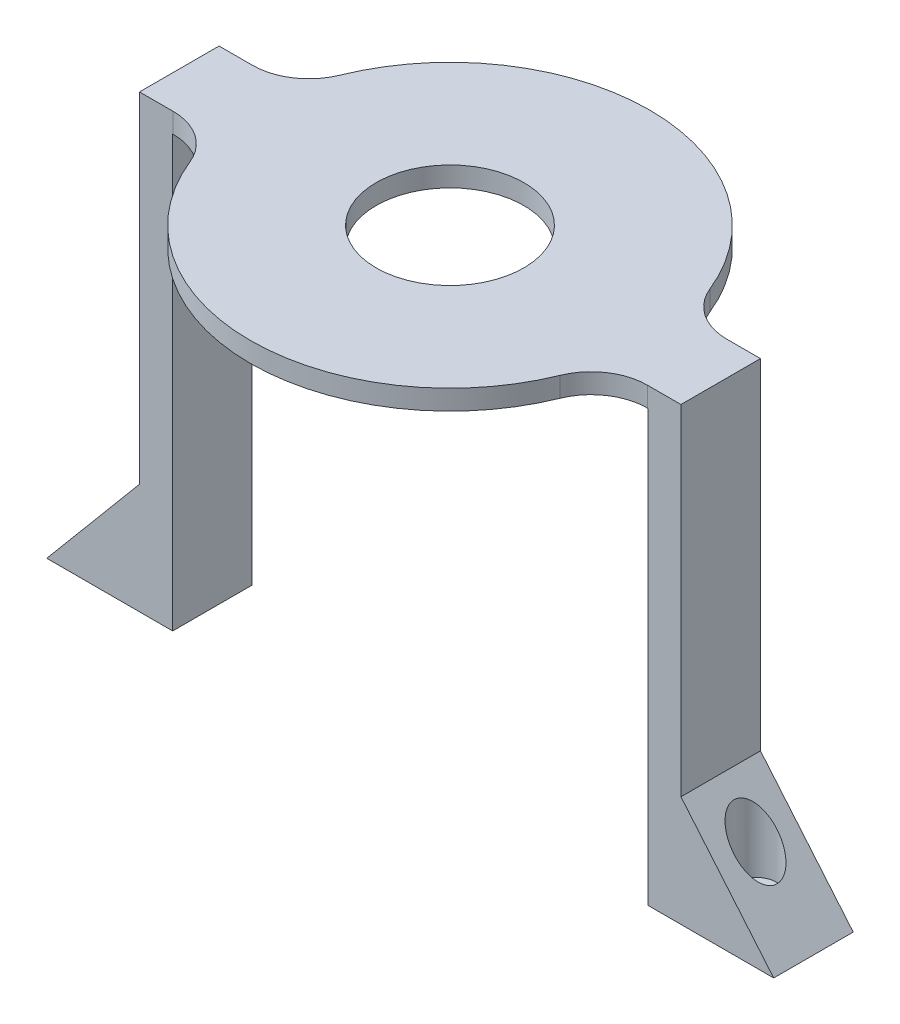
SolidWorks part; units mm, degrees
ref_plane "Front Plane" through (0, 0, 0) normal (0, 0, 1) x (1, 0, 0)
ref_plane "Top Plane" through (0, 0, 0) normal (0, 1, 0) x (1, 0, 0)
ref_plane "Right Plane" through (0, 0, 0) normal (1, 0, 0) x (0, 0, -1)
sketch "Sketch8" plane through (0, 0, 0) normal (0, 1, 0) x (1, 0, 0)
  line L0 (-35.85, 0) -> (35.85, 0) construction
  line L1 (-35.85, -6) -> (-29.5214, -6)
  line L2 (-35.85, 6) -> (-29.5214, 6)
  line L3 (29.5214, 6) -> (35.85, 6)
  line L4 (-35.85, 6) -> (35.85, 6) construction
  line L5 (29.5214, -6) -> (35.85, -6)
  line L6 (-35.85, -6) -> (35.85, -6) construction
  line L7 (-35.85, 6) -> (-35.85, -6)
  line L8 (35.85, 6) -> (35.85, -6)
  circle A0 centre (0, 0) radius 11.15
  arc A1 (29.5214, 6) -> (-29.5214, 6) centre (0, 0) ccw
  arc A2 (-29.5214, -6) -> (29.5214, -6) centre (0, 0) ccw
  point P6 (0, 0)
  dimension "D1" = 60.25
  dimension "D2" = 22.3
  dimension "D3" = 71.7
  dimension "D4" = 6
  dimension "D5" = 6
extrude "Boss-Extrude4" add sketch "Sketch8" along normal blind 3
sketch "Sketch9" plane through (0, 0, 6) normal (0, 0, 1) x (1, 0, 0)
  line L0 (-35.85, 3) -> (-35.85, -64.95)
  line L1 (-35.85, -64.95) -> (-54.85, -64.95)
  line L2 (-54.85, -64.95) -> (-40.85, -48.2654)
  line L3 (-40.85, -48.2654) -> (-40.85, 3)
  line L4 (-40.85, 3) -> (-35.85, 3)
  dimension "D1" = 5
  dimension "D2" = 140
  dimension "D3" = 64.95
  dimension "D4" = 14
extrude "Boss-Extrude5" add sketch "Sketch9" against normal up to surface (12 mm away) up to face at (-32.6857, 1.5, -6)
ref_plane "Plane2" through (0, -48.2654, 0) normal (0, 1, 0) x (0, 0, 1)
sketch "Sketch11" plane through (0, -48.2654, 0) normal (0, 1, 0) x (0, 0, 1)
  line L0 (-6, -40.85) -> (6, -40.85) construction
  circle A0 centre (0, -46.1) radius 3.25
  point P6 (0, -40.85)
  dimension "D1" = 6.5
  dimension "D2" = 5.25
extrude "Cut-Extrude3" cut sketch "Sketch11" against normal blind 13.2
sketch "Sketch14" plane through (0, -48.2654, 0) normal (0, 1, 0) x (0, 0, 1)
  circle A0 centre (0, -46.1) radius 1.7
  dimension "D1" = 3.4
extrude "Cut-Extrude4" cut sketch "Sketch14" against normal through all
mirror "Mirror3" about plane through (0, 0, 0) normal (1, 0, 0) of "Boss-Extrude5", "Cut-Extrude3", "Cut-Extrude4"
fillet "Fillet1" radius 8.5 4 edges at (-29.5214, 1.5, -6) (-29.5214, 1.5, 6) (29.5214, 1.5, -6) (29.5214, 1.5, 6)
equation "\"D2@Sketch11\"=\"D1@Sketch11\"/2+2"
